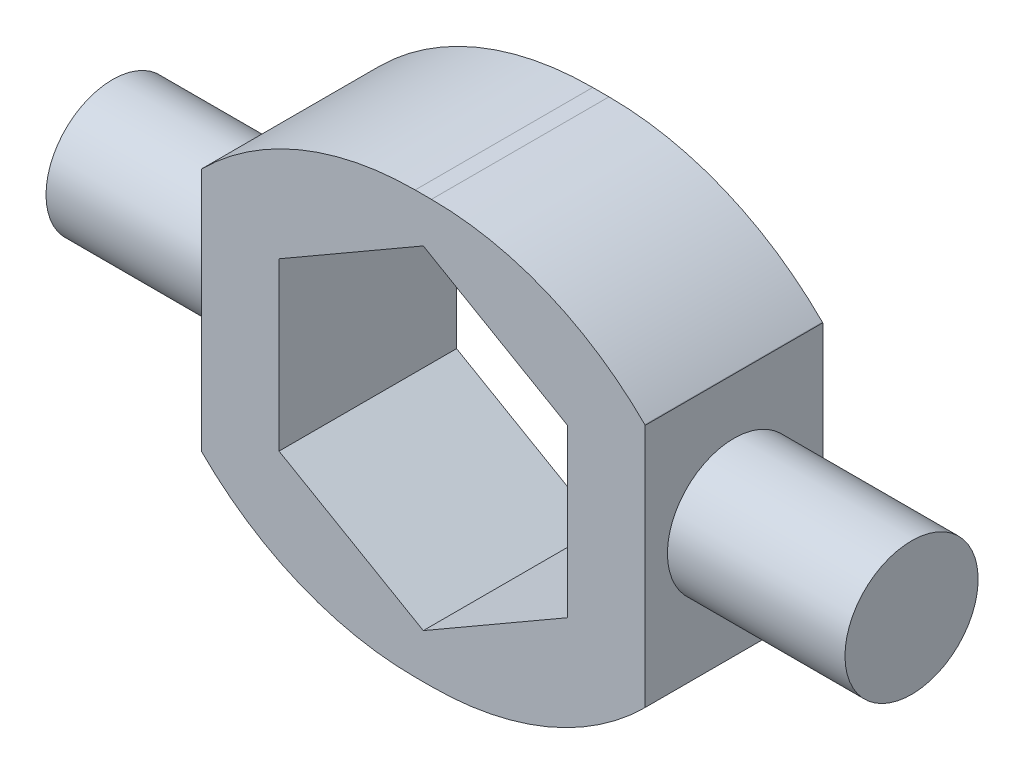
SolidWorks part; units mm, degrees
material "Plain Carbon Steel"
ref_plane "Front Plane" through (0, 0, 0) normal (0, 0, 1) x (1, 0, 0)
ref_plane "Top Plane" through (0, 0, 0) normal (0, 1, 0) x (1, 0, 0)
ref_plane "Right Plane" through (0, 0, 0) normal (1, 0, 0) x (0, 0, -1)
sketch "Sketch1" plane through (0, 0, 0) normal (0, 0, 1) x (1, 0, 0)
  line L1 (0, 0) -> (63.5, 0)
  line L2 (0, 0) -> (0, 60.3603)
  line L3 (0, 60.3603) -> (63.5, 60.3603)
  line L4 (63.5, 0) -> (63.5, 60.3603)
  line L5 (11.1125, 42.0952) -> (11.1125, 18.2651)
  line L6 (11.1125, 18.2651) -> (31.75, 6.35)
  line L7 (31.75, 6.35) -> (52.3875, 18.2651)
  line L8 (52.3875, 18.2651) -> (52.3875, 42.0952)
  line L9 (52.3875, 42.0952) -> (31.75, 54.0103)
  line L10 (31.75, 54.0103) -> (11.1125, 42.0952)
  circle A0 centre (31.75, 30.1801) radius 20.6375 construction
  dimension "D1" = 41.275
  dimension "D2" = 11.1125
  dimension "D3" = 11.1125
  dimension "D4" = 6.35
  dimension "D5" = 6.35
extrude "Boss-Extrude1" add sketch "Sketch1" along normal blind 25.4
chamfer "Chamfer1" distance 12.7 angle 45 4 edges at (63.5, 60.3603, 12.7) (63.5, 0, 12.7) (0, 60.3603, 12.7) (0, 0, 12.7)
sketch "Sketch2" plane through (0, 0, 0) normal (-1, 0, 0) x (0, 0, 1)
  line L2 (0, 47.6603) -> (25.4, 12.7) construction
  circle A0 centre (12.7, 30.1801) radius 9.525
  dimension "D1" = 19.05
extrude "Boss-Extrude2" add sketch "Sketch2" along normal blind 25.4
ref_plane "Plane1" through (31.75, 0, 0) normal (1, 0, 0) x (0, 0, -1)
mirror "Mirror1" about plane through (31.75, 0, 0) normal (1, 0, 0) of "Boss-Extrude2"
fillet "Fillet1" radius 43.18 4 edges at (50.8, 60.3603, 12.7) (12.7, 60.3603, 12.7) (50.8, 0, 12.7) (12.7, 0, 12.7)
